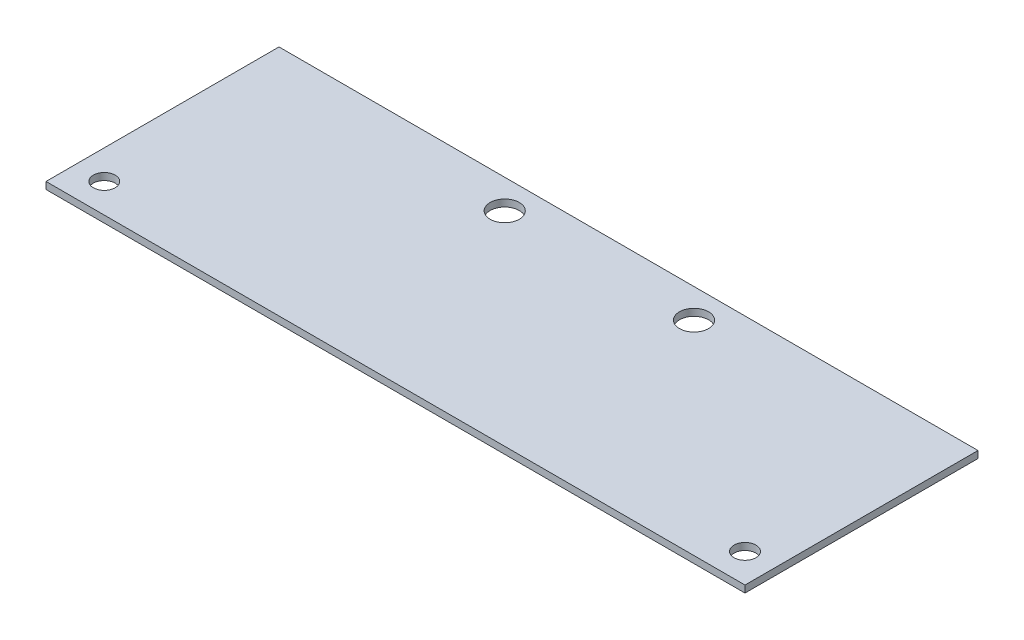
SolidWorks part; units mm, degrees
material "1023 Carbon Steel Sheet (SS)"
ref_plane "Front Plane" through (0, 0, 0) normal (0, 0, 1) x (1, 0, 0)
ref_plane "Top Plane" through (0, 0, 0) normal (0, 1, 0) x (1, 0, 0)
ref_plane "Right Plane" through (0, 0, 0) normal (1, 0, 0) x (0, 0, -1)
sketch "Sketch1" plane through (0, 0, 0) normal (0, 1, 0) x (1, 0, 0)
  line L1 (0, 0) -> (152.4, 0)
  line L2 (0, 0) -> (0, 50.8)
  line L3 (0, 50.8) -> (152.4, 50.8)
  line L4 (152.4, 0) -> (152.4, 50.8)
  circle A0 centre (6.35, 6.35) radius 2.3876
  circle A1 centre (55.5625, 44.45) radius 3.175
  circle A2 centre (146.05, 6.35) radius 2.3876
  circle A3 centre (96.8375, 44.45) radius 3.175
  dimension "D2" = 4.7752
  dimension "D5" = 6.35
  dimension "D6" = 38.1
  dimension "D1" = 4.7752
  dimension "D8" = 6.35
  dimension "D9" = 6.35
  dimension "D11" = 41.275
  dimension "D3" = 6.35
  dimension "D4" = 6.35
  dimension "D7" = 139.7
  dimension "D10" = 6.35
  dimension "D12" = 152.4
  dimension "D13" = 55.5625
extrude "Boss-Extrude1" add sketch "Sketch1" along normal blind 1.524
